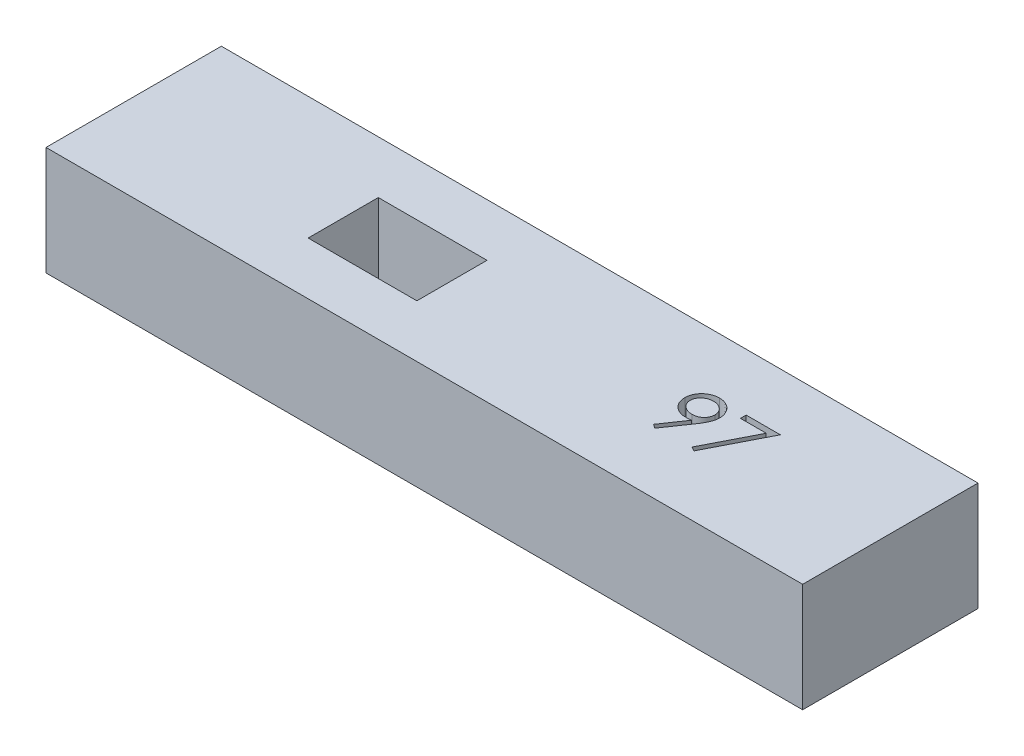
SolidWorks part; units mm, degrees
ref_plane "Front Plane" through (0, 0, 0) normal (0, 0, 1) x (1, 0, 0)
ref_plane "Top Plane" through (0, 0, 0) normal (0, 1, 0) x (1, 0, 0)
ref_plane "Right Plane" through (0, 0, 0) normal (1, 0, 0) x (0, 0, -1)
sketch "Sketch2" plane through (0, 0, 0) normal (0, 1, 0) x (1, 0, 0)
  line L0 (0, 0) -> (6.2, 0)
  line L1 (6.2, 0) -> (6.2, 4)
  line L2 (6.2, 4) -> (0, 4)
  line L3 (0, 4) -> (0, 0)
  line L5 (-0.1, 7) -> (6.2, 7)
  line L8 (6.2, -3) -> (-0.1, -3)
  line L10 (6.2, 7) -> (31.2, 7)
  line L11 (31.2, 7) -> (31.2, -3)
  line L12 (31.2, -3) -> (6.2, -3)
  line L13 (-0.1, -3) -> (-11.95, -3)
  line L14 (-11.95, -3) -> (-11.95, 7)
  line L15 (-11.95, 7) -> (-0.1, 7)
  dimension "D1" = 6.2
  dimension "D2" = 4
  dimension "D3" = 3
  dimension "D4" = 3
  dimension "D5" = 25
  dimension "D6" = 11.85
extrude "Boss-Extrude1" add sketch "Sketch2" along normal blind 6.2
sketch "Sketch3" plane through (0, 6.2, 0) normal (0, 1, 0) x (1, 0, 0)
  text T0 "97"
  point P1 (18.1049, 1.4198)
  point P2 (18.4174, -0.4547)
  point P3 (18.462, 0.5718)
extrude "Cut-Extrude1" cut sketch "Sketch3" against normal blind 1
